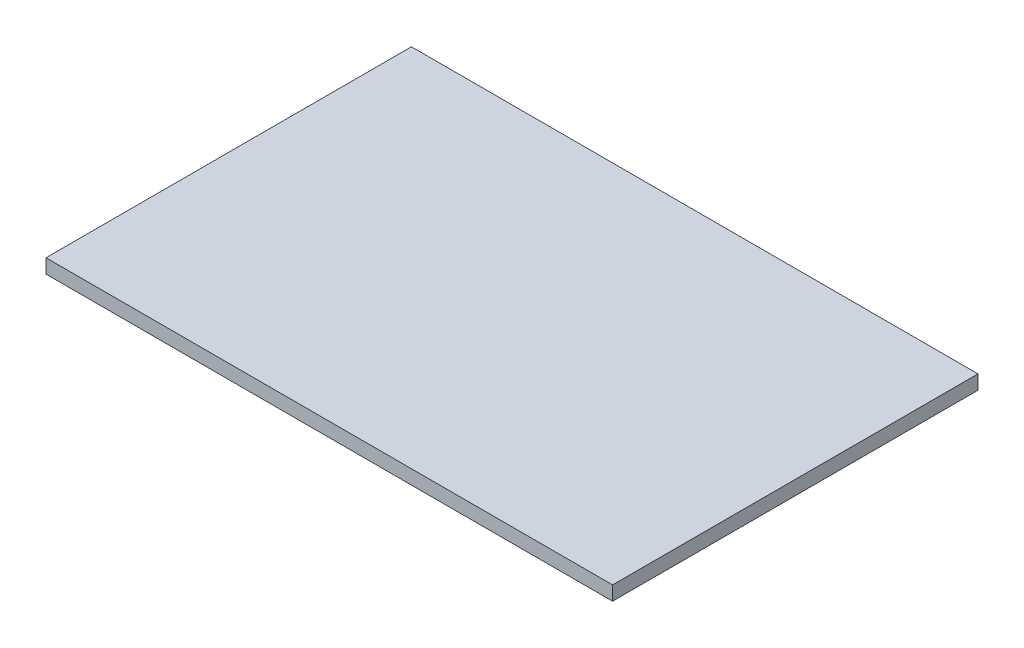
SolidWorks part; units mm, degrees
ref_plane "Face" through (0, 0, 0) normal (0, 0, 1) x (1, 0, 0)
ref_plane "Dessus" through (0, 0, 0) normal (0, 1, 0) x (1, 0, 0)
ref_plane "Droite" through (0, 0, 0) normal (1, 0, 0) x (0, 0, -1)
sketch "Esquisse1" plane through (0, 0, 0) normal (0, 1, 0) x (1, 0, 0)
  line L1 (0, 0) -> (400, 0)
  line L2 (0, 0) -> (0, 258)
  line L3 (0, 258) -> (400, 258)
  line L4 (400, 0) -> (400, 258)
  dimension "D1" = 258
  dimension "D2" = 400
extrude "Extrusion1" add sketch "Esquisse1" along normal blind 10
